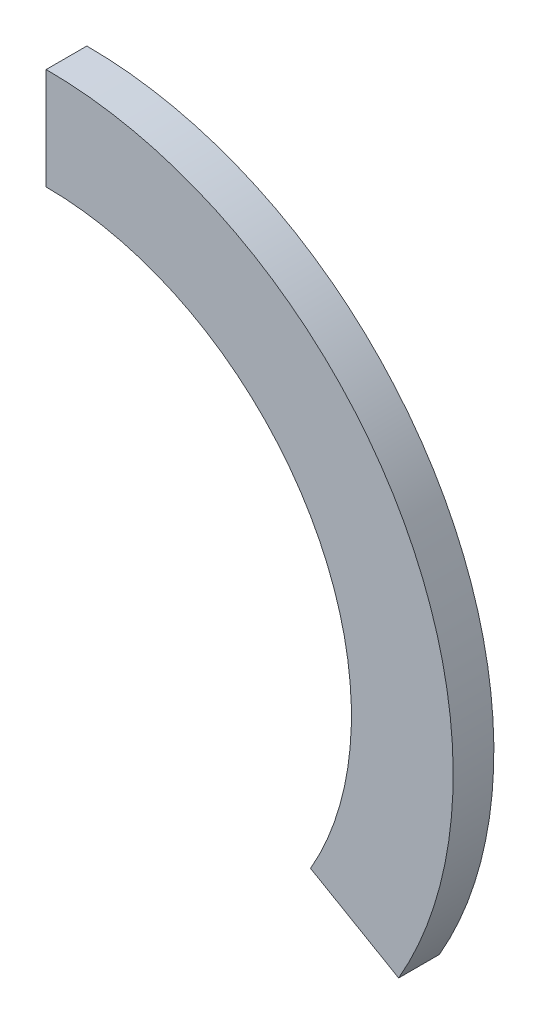
SolidWorks part; units mm, degrees
ref_plane "Front Plane" through (0, 0, 0) normal (0, 0, 1) x (1, 0, 0)
ref_plane "Top Plane" through (0, 0, 0) normal (0, 1, 0) x (1, 0, 0)
ref_plane "Right Plane" through (0, 0, 0) normal (1, 0, 0) x (0, 0, -1)
sketch "Sketch2" plane through (0, 0, 0) normal (0, 0, 1) x (1, 0, 0)
  line L0 (0, 60) -> (0, 80)
  line L1 (51.9615, -30) -> (69.282, -40)
  arc A0 (69.282, -40) -> (0, 80) centre (0, 0) ccw
  arc A1 (51.9615, -30) -> (0, 60) centre (0, 0) ccw
  point P1 (-3.1675, 0.7939)
  point P10 (0, 0)
  dimension "D1" = 20
  dimension "D2" = 60
  dimension "D3" = 2
extrude "Boss-Extrude2" add sketch "Sketch2" along normal blind 8 contours A1 L0 A0 L1
